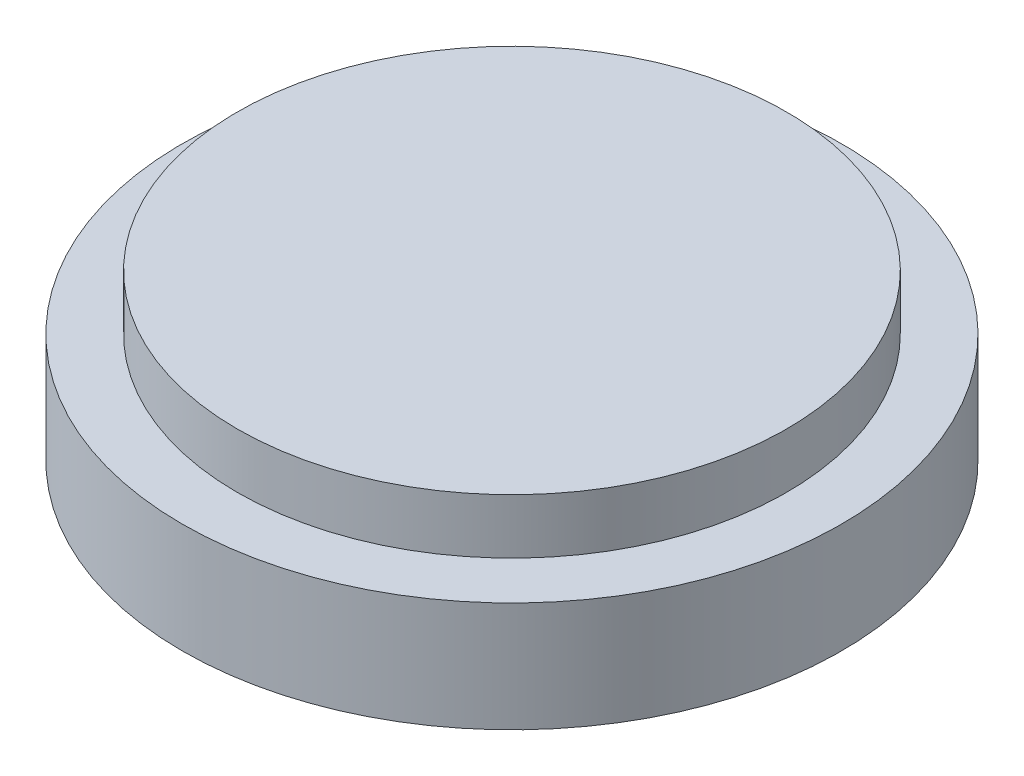
SolidWorks part; units mm, degrees
material "Alloy Steel"
ref_plane "Front Plane" through (0, 0, 0) normal (0, 0, 1) x (1, 0, 0)
ref_plane "Top Plane" through (0, 0, 0) normal (0, 1, 0) x (1, 0, 0)
ref_plane "Right Plane" through (0, 0, 0) normal (1, 0, 0) x (0, 0, -1)
sketch "Sketch1" plane through (0, 0, 0) normal (0, 1, 0) x (1, 0, 0)
  circle A0 centre (0, 0) radius 600
  dimension "D1" = 1200
extrude "Boss-Extrude1" add sketch "Sketch1" along normal blind 200
sketch "Sketch3" plane through (0, 200, 0) normal (0, 1, 0) x (1, 0, 0)
  circle A0 centre (0, 0) radius 500
extrude "Boss-Extrude2" add sketch "Sketch3" along normal blind 100
sketch "Sketch4" plane through (0, 0, 0) normal (0, -1, 0) x (-1, 0, 0)
  point P0 (0, 0)
